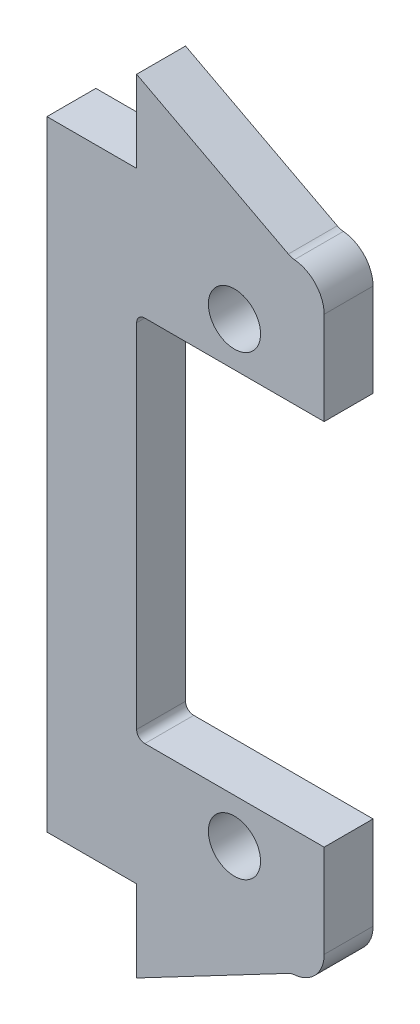
SolidWorks part; units mm, degrees
material "ﾁｰｸ材"
ref_plane "正面" through (0, 0, 0) normal (0, 0, 1) x (1, 0, 0)
ref_plane "平面" through (0, 0, 0) normal (0, 1, 0) x (1, 0, 0)
ref_plane "右側面" through (0, 0, 0) normal (1, 0, 0) x (0, 0, -1)
sketch "ｽｹｯﾁ1" plane through (0, 0, 0) normal (0, 0, 1) x (1, 0, 0)
  line L0 (0, -19) -> (0, 19)
  line L1 (0, 19) -> (17, 19)
  line L2 (17, 19) -> (17, 11.3)
  line L3 (17, 11.3) -> (5.5, 11.3)
  line L4 (5.5, 11.3) -> (5.5, -11.3)
  line L5 (5.5, -11.3) -> (17, -11.3)
  line L6 (17, -11.3) -> (17, -19)
  line L7 (17, -19) -> (0, -19)
  line L8 (11.5, 19) -> (11.5, -19) construction
  line L9 (2.75, 19) -> (2.75, -19) construction
  line L10 (0, 0) -> (5.5, 0) construction
  circle A0 centre (11.5, 14) radius 1.6
  circle A1 centre (11.5, -14) radius 1.6
  circle A2 centre (2.75, 10) radius 1.6 construction
  circle A3 centre (2.75, -10) radius 1.6 construction
  point P4 (0, 0)
  dimension "D9" = 3.2
  dimension "D1" = 11.5
  dimension "D2" = 5.5
  dimension "D3" = 38
  dimension "D5" = 22.6
  dimension "D6" = 6
  dimension "D7" = 28
  dimension "D8" = 14
  dimension "D10" = 2.75
  dimension "D11" = 9
  dimension "D12" = 9
extrude "ﾎﾞｽ - 押し出し1" add sketch "ｽｹｯﾁ1" along normal blind 3
fillet "ﾌｨﾚｯﾄ1" radius 0.5 2 edges at (5.5, -11.3, 1.5) (5.5, 11.3, 1.5)
fillet "ﾌｨﾚｯﾄ2" radius 2 2 edges at (17, 19, 1.5) (17, -19, 1.5)
sketch "ｽｹｯﾁ2" plane through (0, 0, 3) normal (0, 0, 1) x (1, 0, 0)
  line L0 (5.5, 19) -> (5.5, 24)
  line L1 (15, 19) -> (0, 19) construction
  line L2 (5.5, 24) -> (15, 19)
  line L3 (15, 19) -> (5.5, 19)
  line L4 (5.5, -19) -> (5.5, -24)
  line L5 (0, -19) -> (15, -19) construction
  line L6 (5.5, -24) -> (15, -19)
  line L7 (15, -19) -> (5.5, -19)
  line L8 (5.5, -10.8) -> (5.5, 10.8) construction
  dimension "D1" = 5
  dimension "D2" = 5
extrude "ﾎﾞｽ - 押し出し2" add sketch "ｽｹｯﾁ2" against normal up to surface (3 mm away) up to face at (13.1, 14, 0)
fillet "ﾌｨﾚｯﾄ3" radius 1 2 edges at (15, -19, 1.5) (15, 19, 1.5)
equation "\"D2@ｽｹｯﾁ2\"=\"D1@ｽｹｯﾁ2\""
